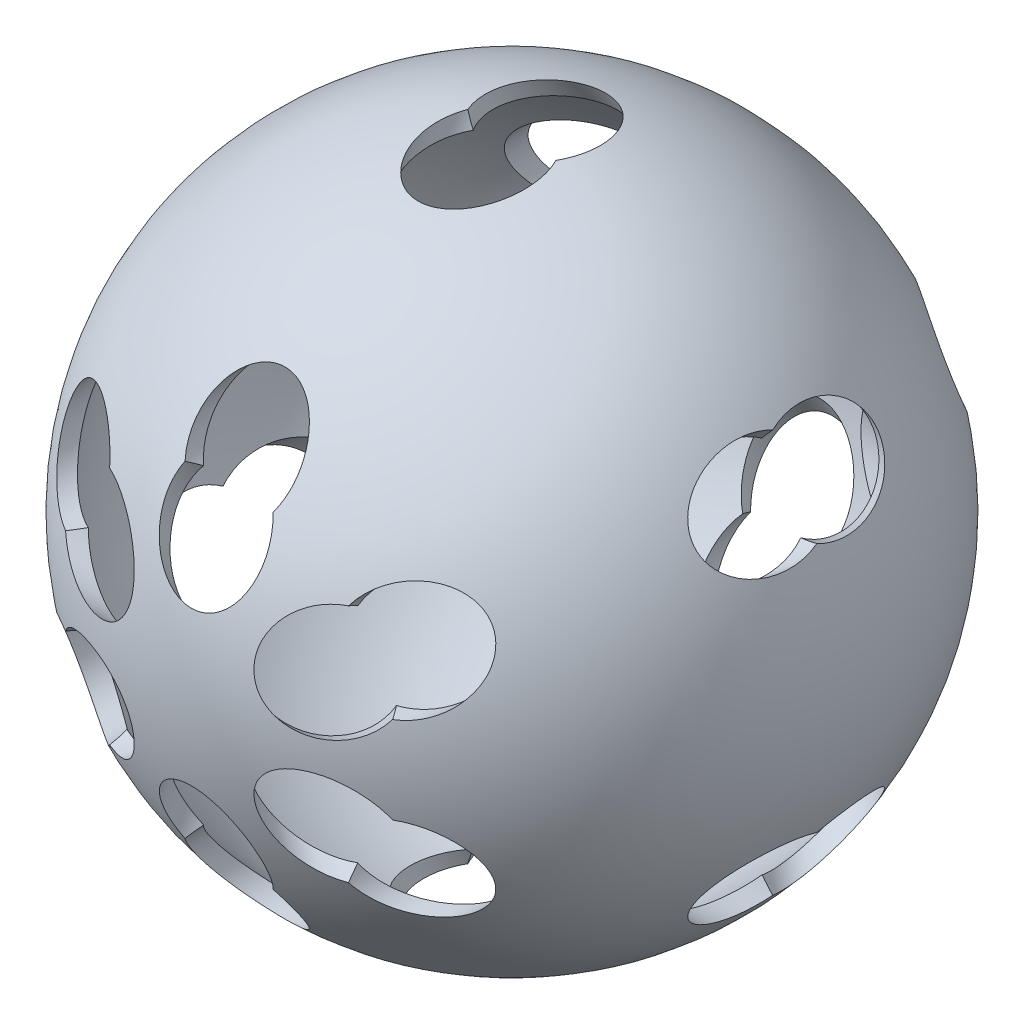
SolidWorks part; units mm, degrees
material "ABS"
ref_plane "Front Plane" through (0, 0, 0) normal (0, 0, 1) x (1, 0, 0)
ref_plane "Top Plane" through (0, 0, 0) normal (0, 1, 0) x (1, 0, 0)
ref_plane "Right Plane" through (0, 0, 0) normal (1, 0, 0) x (0, 0, -1)
sketch "Sketch1" plane through (0, 0, 0) normal (0, 0, 1) x (1, 0, 0)
  line L0 (0, 61.9125) -> (0, -61.9125) construction
  arc A0 (0, 61.9125) -> (0, -61.9125) centre (0, 0) cw
  point P8 (0, 0)
  dimension "D1" = 123.825
revolve "Revolve-Thin1" add sketch "Sketch1" angle 360 about L0
sketch "Sketch2" plane through (0, 0, 0) normal (0, 0, 1) x (1, 0, 0)
  line L4 (0, 35.3909) -> (-50.8, 35.3909) construction
  circle A0 centre (0, 35.3909) radius 9.525
  circle A4 centre (0, 0) radius 61.9125 construction
  dimension "D1" = 19.05
  dimension "D3" = 50.8
extrude "Cut-Extrude1" cut sketch "Sketch2" along normal through all contours A0
sketch "Sketch8" plane through (0, 0, 0) normal (0, 1, 0) x (1, 0, 0)
  line L0 (0, 0) -> (0, 61.9125)
  line L1 (0, 0) -> (-61.9125, 0)
  circle A0 centre (0, 0) radius 61.9125 construction
pattern_circular "CirPattern29" count 6 over 360 about axis through (0, 0, 0) along (-1, 0, 0) of "Cut-Extrude1"
pattern_circular "CirPattern30" count 6 over 360 about axis through (0, 0, 0) along (0, 0, 1) of "CirPattern29", "Cut-Extrude1"
